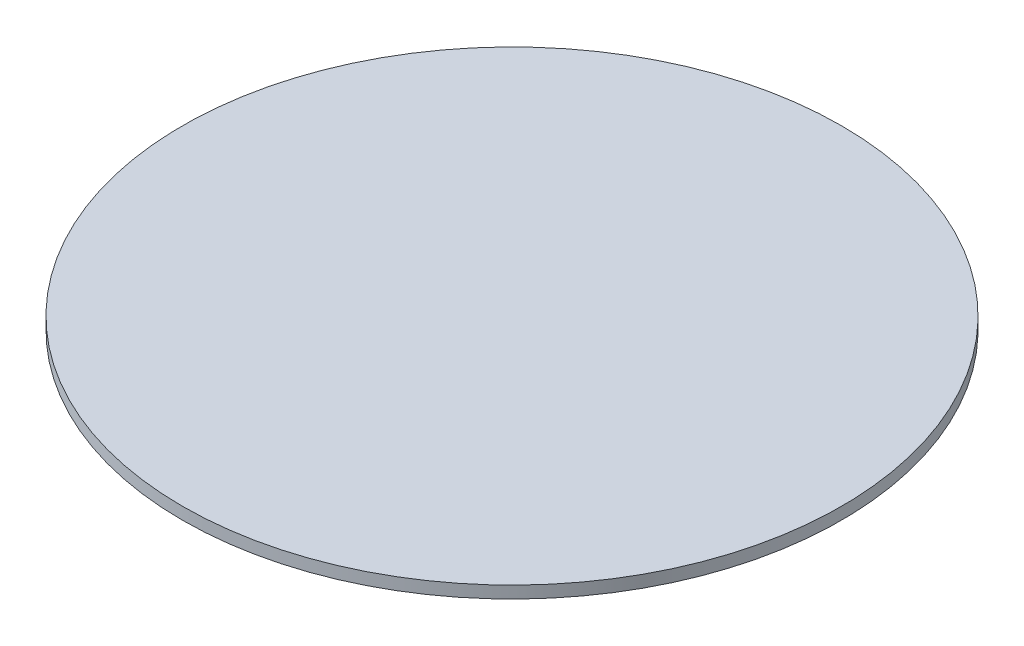
SolidWorks part; units mm, degrees
ref_plane "Front Plane" through (0, 0, 0) normal (0, 0, 1) x (1, 0, 0)
ref_plane "Top Plane" through (0, 0, 0) normal (0, 1, 0) x (1, 0, 0)
ref_plane "Right Plane" through (0, 0, 0) normal (1, 0, 0) x (0, 0, -1)
sketch "Sketch1" plane through (0, 0, 0) normal (0, 1, 0) x (1, 0, 0)
  circle A0 centre (0, 0) radius 2076.2
  dimension "D1" = 4152.4
extrude "Boss-Extrude1" add sketch "Sketch1" along normal blind 76.2
